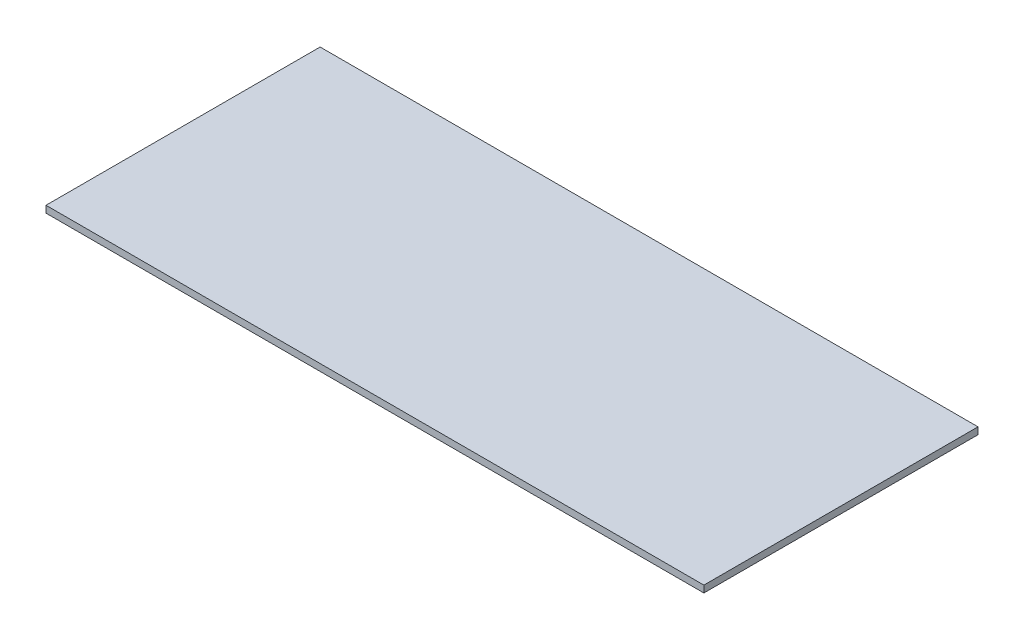
SolidWorks part; units mm, degrees
ref_plane "Front Plane" through (0, 0, 0) normal (0, 0, 1) x (1, 0, 0)
ref_plane "Top Plane" through (0, 0, 0) normal (0, 1, 0) x (1, 0, 0)
ref_plane "Right Plane" through (0, 0, 0) normal (1, 0, 0) x (0, 0, -1)
sketch "Sketch1" plane through (0, 0, 0) normal (0, 1, 0) x (1, 0, 0)
  line L1 (144, -60) -> (-144, -60)
  line L2 (144, -60) -> (144, 60)
  line L3 (144, 60) -> (-144, 60)
  line L4 (-144, -60) -> (-144, 60)
  line L5 (144, -60) -> (-144, 60) construction
  line L6 (144, 60) -> (-144, -60) construction
  point P0 (0, 0)
  dimension "D1" = 288
  dimension "D2" = 120
extrude "Boss-Extrude1" add sketch "Sketch1" along normal blind 3
